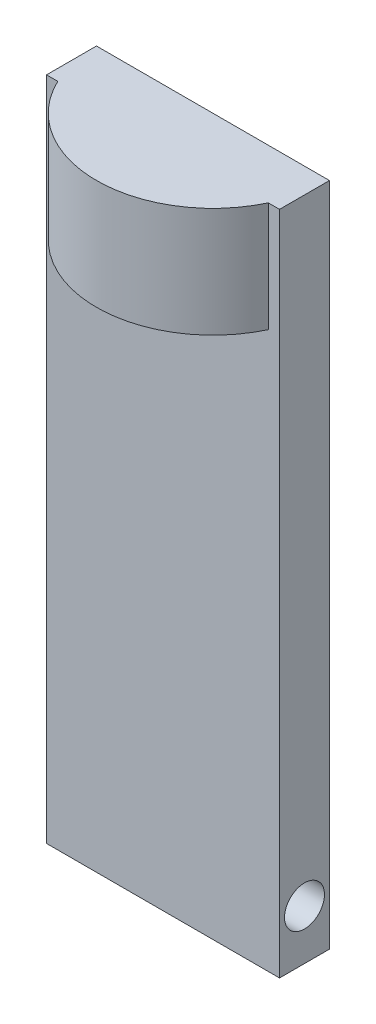
SolidWorks part; units mm, degrees
ref_plane "Front Plane" through (0, 0, 0) normal (0, 0, 1) x (1, 0, 0)
ref_plane "Top Plane" through (0, 0, 0) normal (0, 1, 0) x (1, 0, 0)
ref_plane "Right Plane" through (0, 0, 0) normal (1, 0, 0) x (0, 0, -1)
sketch "Sketch1" plane through (0, 0, 0) normal (0, 0, 1) x (1, 0, 0)
  line L1 (-35, 100) -> (35, 100)
  line L2 (-35, 100) -> (-35, -100)
  line L3 (-35, -100) -> (35, -100)
  line L4 (35, 100) -> (35, -100)
  line L5 (-35, 100) -> (35, -100) construction
  line L6 (-35, -100) -> (35, 100) construction
  point P0 (0, 0)
  dimension "D1" = 200
  dimension "D2" = 70
extrude "Boss-Extrude4" add sketch "Sketch1" along normal blind 15
sketch "Sketch9" plane through (35, 0, 0) normal (1, 0, 0) x (0, 0, -1)
  line L0 (-15, -100) -> (0, -100) construction
  circle A0 centre (-7.5, -85) radius 6
  dimension "D1" = 15
  dimension "D2" = 12
extrude "Cut-Extrude1" cut sketch "Sketch9" against normal through all
sketch "Sketch10" plane through (0, 100, 0) normal (0, 1, 0) x (1, 0, 0)
  line L0 (35, 0) -> (-35, 0) construction
  line L1 (-35, -15) -> (35, -15)
  circle A0 centre (0, 0) radius 35
  dimension "D1" = 70
extrude "Boss-Extrude5" add sketch "Sketch10" against normal blind 33 contours L1 A0
